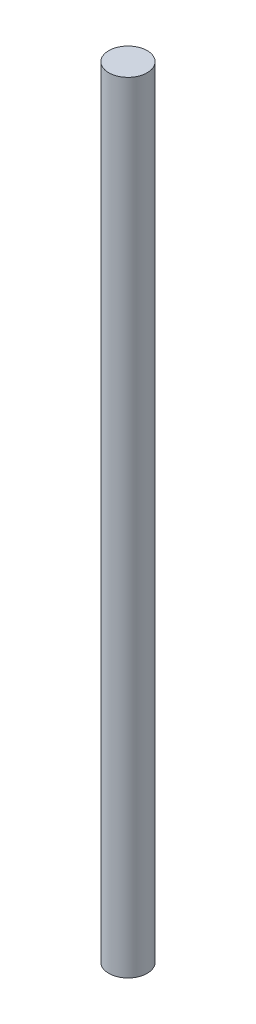
SolidWorks part; units mm, degrees
ref_plane "Front Plane" through (0, 0, 0) normal (0, 0, 1) x (1, 0, 0)
ref_plane "Top Plane" through (0, 0, 0) normal (0, 1, 0) x (1, 0, 0)
ref_plane "Right Plane" through (0, 0, 0) normal (1, 0, 0) x (0, 0, -1)
sketch "Sketch1" plane through (0, 0, 0) normal (0, 1, 0) x (1, 0, 0)
  circle A0 centre (0, 0) radius 2.4511
  dimension "D1" = 4.9022
extrude "Boss-Extrude1" add sketch "Sketch1" along normal blind 99.568
